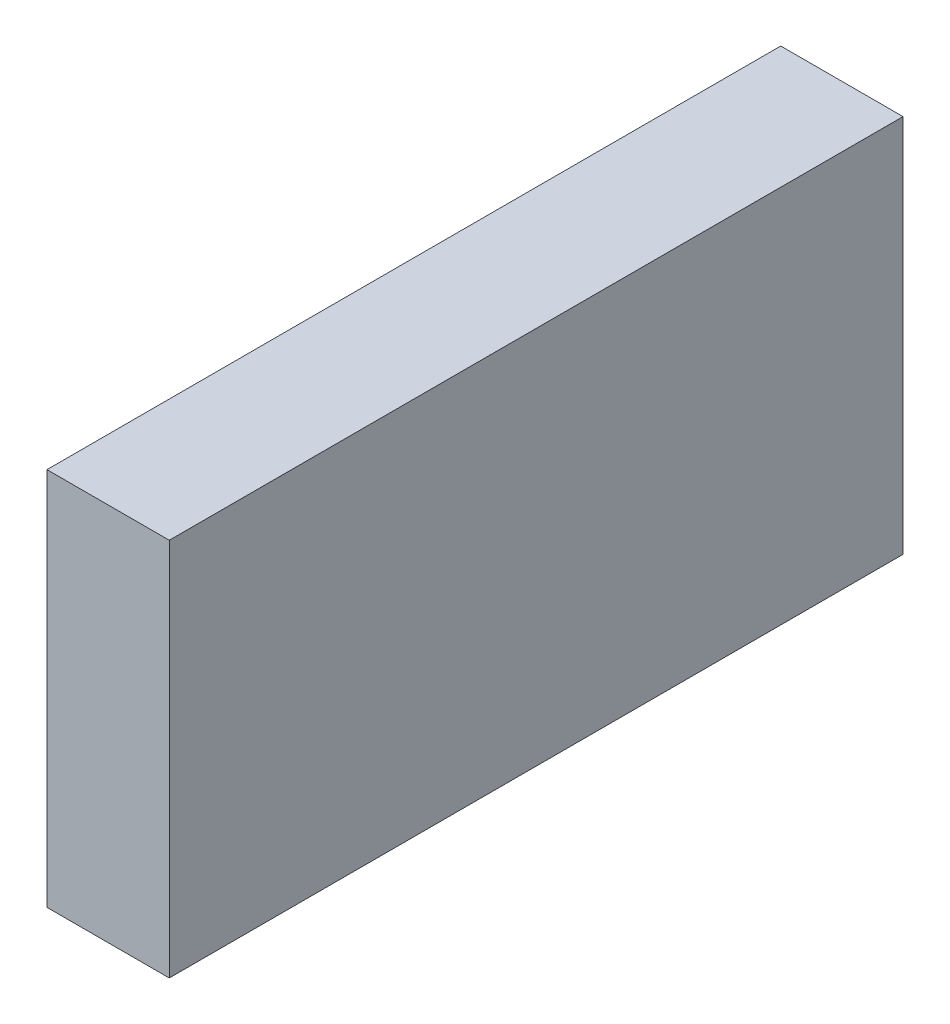
SolidWorks part; units mm, degrees
material "Maple"
ref_plane "Front Plane" through (0, 0, 0) normal (0, 0, 1) x (1, 0, 0)
ref_plane "Top Plane" through (0, 0, 0) normal (0, 1, 0) x (1, 0, 0)
ref_plane "Right Plane" through (0, 0, 0) normal (1, 0, 0) x (0, 0, -1)
sketch "Sketch1" plane through (0, 0, 0) normal (1, 0, 0) x (0, 0, -1)
  line L0 (0, 0) -> (76.2, 0)
  line L1 (0, 0) -> (0, 39.37)
  line L2 (76.2, 0) -> (76.2, 39.37)
  line L3 (0, 39.37) -> (76.2, 39.37)
  dimension "D1" = 76.2
  dimension "D2" = 39.37
extrude "Boss-Extrude1" add sketch "Sketch1" along normal blind 12.7
